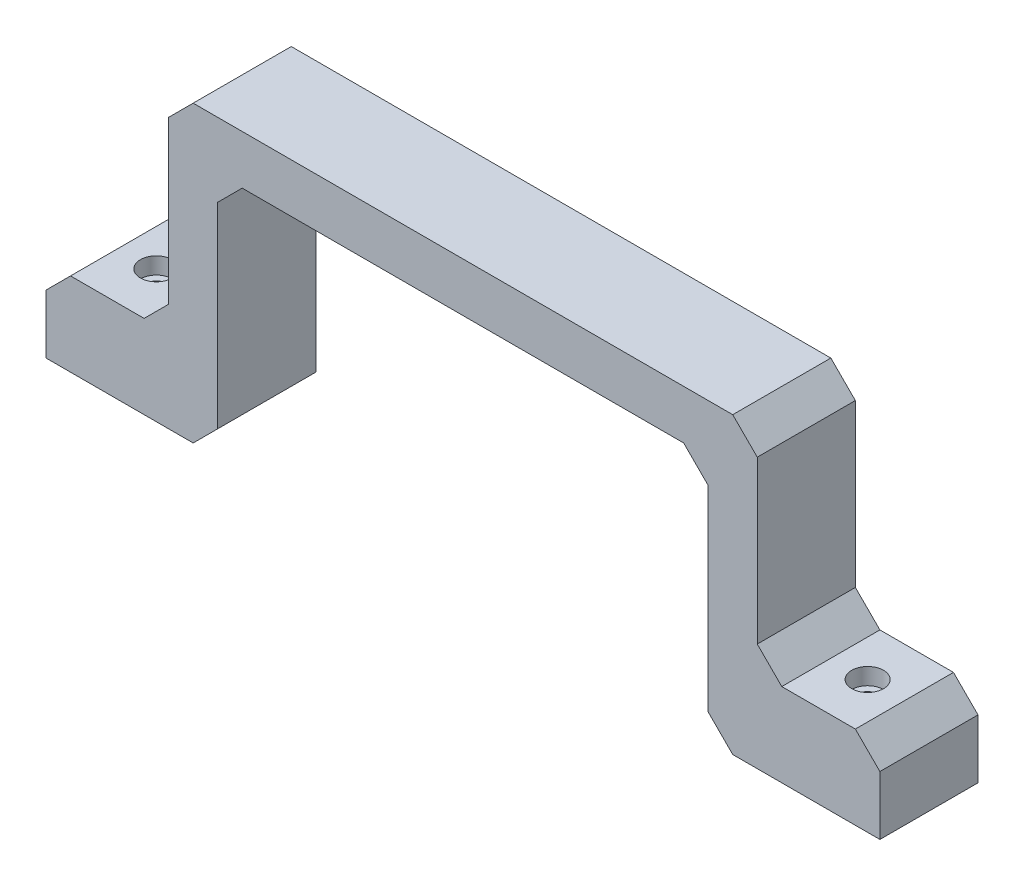
SolidWorks part; units mm, degrees
material "Allzweck-PBT"
ref_plane "Ebene vorne" through (0, 0, 0) normal (0, 0, 1) x (1, 0, 0)
ref_plane "Ebene oben" through (0, 0, 0) normal (0, 1, 0) x (1, 0, 0)
ref_plane "Ebene rechts" through (0, 0, 0) normal (1, 0, 0) x (0, 0, -1)
sketch "Skizze1" plane through (0, 0, 0) normal (0, 0, 1) x (1, 0, 0)
  line L0 (5, 0) -> (20, 0)
  line L1 (25, 5) -> (25, 38)
  line L2 (30, 43) -> (140, 43)
  line L3 (145, 38) -> (145, 5)
  line L4 (150, 0) -> (165, 0)
  line L5 (170, -5) -> (170, -17)
  line L6 (170, -17) -> (140, -17)
  line L7 (135, -12) -> (135, 28)
  line L8 (130, 33) -> (40, 33)
  line L9 (35, 28) -> (35, -12)
  line L10 (30, -17) -> (0, -17)
  line L11 (0, -17) -> (0, -5)
  line L12 (25, 38) -> (30, 43)
  line L13 (140, 43) -> (145, 38)
  line L14 (135, 28) -> (130, 33)
  line L15 (40, 33) -> (35, 28)
  line L16 (20, 0) -> (25, 5)
  line L17 (35, -12) -> (30, -17)
  line L18 (140, -17) -> (135, -12)
  line L19 (145, 5) -> (150, 0)
  line L20 (0, -5) -> (5, 0)
  line L21 (165, 0) -> (170, -5)
  point P0 (0, 0)
  point P1 (25, 0)
  point P3 (170, 0)
  point P4 (25, 43)
  point P5 (145, 43)
  point P6 (145, 0)
  point P9 (135, -17)
  point P10 (135, 33)
  point P11 (35, 33)
  point P12 (35, -17)
  dimension "D1" = 100
  dimension "D2" = 10
  dimension "D3" = 10
  dimension "D4" = 10
  dimension "D5" = 50
  dimension "D6" = 25
  dimension "D7" = 25
  dimension "D8" = 17
extrude "Aufsatz-Linear austragen1" add sketch "Skizze1" along normal blind 20 contours L2 L13 L3 L19 L4 L21 L5 L6 L18 L7 L14 L8 L15 L9 L17 L10 L11 L20 L0 L16 L1 L12
hole_wizard "Stirnsenkung für M3 Zylinderschraube mit Innensechskant2" positions "Skizze4" profile "Skizze5" counterbore size "M3" standard "DIN" end condition up to next
sketch "Skizze4" plane through (0, 0, 0) normal (0, 1, 0) x (1, 0, 0)
  line L0 (5, 0) -> (20, 0) construction
  line L1 (150, 0) -> (165, 0) construction
  line L2 (5, -20) -> (5, 0) construction
  line L3 (150, -20) -> (150, 0) construction
  point P0 (157.5, -10)
  point P2 (12.5, -10)
  dimension "D1" = 10
  dimension "D2" = 10
  dimension "D3" = 7.5
  dimension "D4" = 7.5
sketch "Skizze5" plane through (157.5, 0, 10) normal (1, 0, 0) x (0, 0, 1)
  line L0 (0, 0) -> (0, 17)
  line L1 (0, 17) -> (1.8, 17)
  line L3 (1.8, 17) -> (1.8, 3.4)
  line L4 (1.8, 3.4) -> (3.25, 3.4)
  line L5 (3.25, 3.4) -> (3.25, 0)
  line L7 (3.25, 0) -> (0, 0)
  line L11 (0, -6.35) -> (0, 107.95) construction
  dimension "Bohrerdurchmesser" = 3.6
  dimension "Bohrungstiefe" = 17
  dimension "Senkdurchmesser2" = 6.5
  dimension "Senktiefe2" = 3.4
